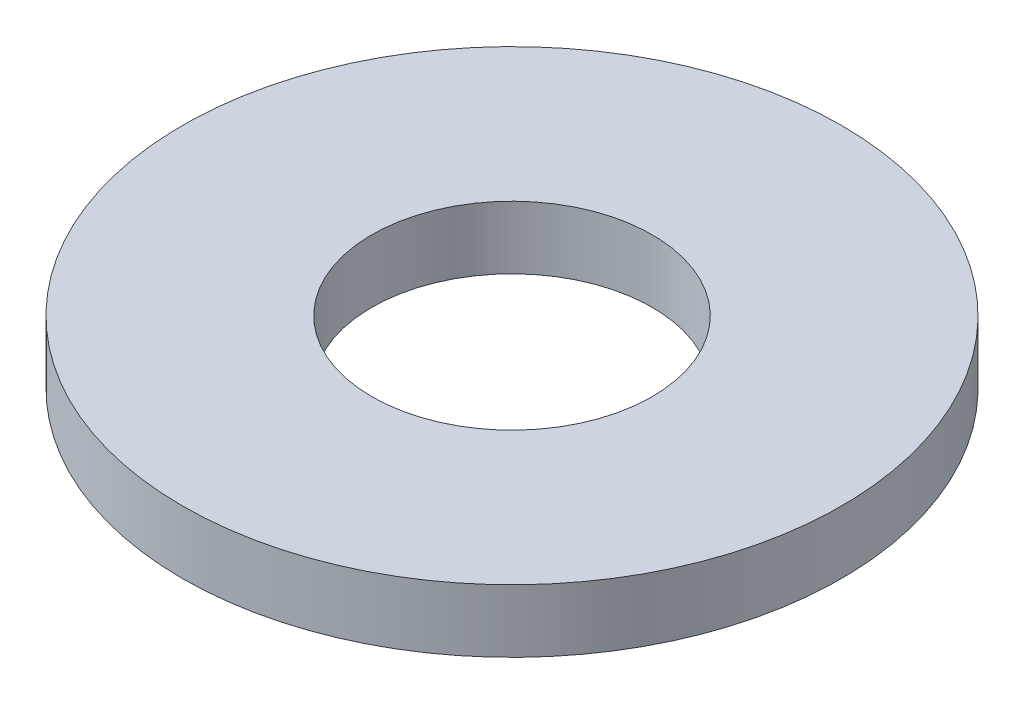
SolidWorks part; units mm, degrees
material "AISI 304"
ref_plane "Front Plane" through (0, 0, 0) normal (0, 0, 1) x (1, 0, 0)
ref_plane "Top Plane" through (0, 0, 0) normal (0, 1, 0) x (1, 0, 0)
ref_plane "Right Plane" through (0, 0, 0) normal (1, 0, 0) x (0, 0, -1)
sketch "Sketch1" plane through (0, 0, 0) normal (0, 1, 0) x (1, 0, 0)
  circle A0 centre (0, 0) radius 9.3266
  circle A1 centre (0, 0) radius 3.9688
  dimension "D1" = 7.9375
  dimension "D2" = 18.6531
extrude "Boss-Extrude1" add sketch "Sketch1" along normal blind 1.78
